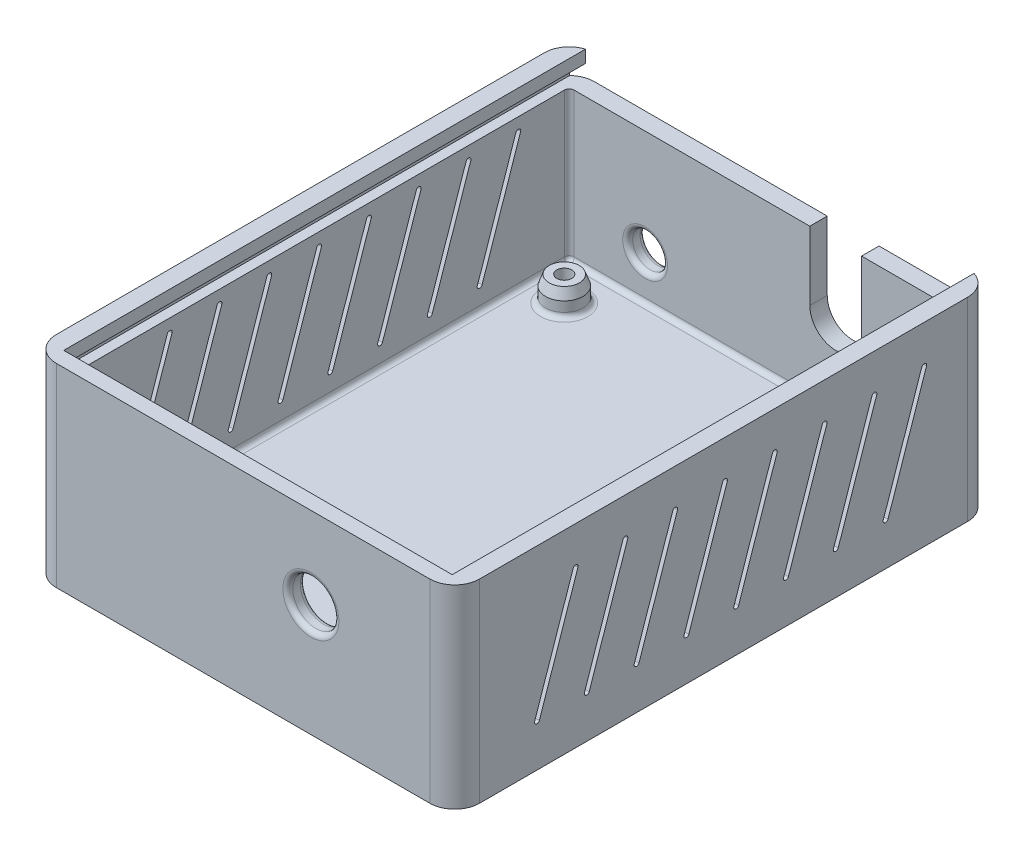
SolidWorks part; units mm, degrees
ref_plane "Front" through (0, 0, 0) normal (0, 0, 1) x (1, 0, 0)
ref_plane "Top" through (0, 0, 0) normal (0, 1, 0) x (1, 0, 0)
ref_plane "Right" through (0, 0, 0) normal (1, 0, 0) x (0, 0, -1)
sketch "Sketch1" plane through (0, 0, 0) normal (0, 1, 0) x (1, 0, 0)
  line L1 (-56.1278, 52.2306) -> (28.8722, 52.2306)
  line L2 (-56.1278, 52.2306) -> (-56.1278, -55.7694)
  line L3 (-56.1278, -55.7694) -> (28.8722, -55.7694)
  line L4 (28.8722, 52.2306) -> (28.8722, -55.7694)
  dimension "D1" = 85
  dimension "D2" = 108
extrude "Boss-Extrude1" add sketch "Sketch1" along normal blind 4
sketch "Sketch2" plane through (0, 4, 0) normal (0, 1, 0) x (1, 0, 0)
  line L0 (-52.6278, 48.7306) -> (-52.6278, -52.2694)
  line L1 (-56.1278, 52.2306) -> (28.8722, 52.2306)
  line L2 (-56.1278, 52.2306) -> (-56.1278, -55.7694)
  line L3 (-56.1278, -55.7694) -> (28.8722, -55.7694)
  line L4 (28.8722, 52.2306) -> (28.8722, -55.7694)
  line L5 (-52.6278, -52.2694) -> (25.3722, -52.2694)
  line L6 (25.3722, 48.7306) -> (25.3722, -52.2694)
  line L7 (-52.6278, 48.7306) -> (25.3722, 48.7306)
  dimension "D1" = 3.5
extrude "Boss-Extrude2" add sketch "Sketch2" along normal blind 35
sketch "Sketch3" plane through (0, 4, 0) normal (0, 1, 0) x (1, 0, 0)
  line L0 (25.3722, 48.7306) -> (-52.6278, 48.7306) construction
  line L1 (-52.6278, 48.7306) -> (-52.6278, -52.2694) construction
  circle A0 centre (-45.6278, 40.7306) radius 3.75
  circle A1 centre (18.3722, 40.7306) radius 3.75
  circle A2 centre (18.3722, -45.2694) radius 3.75
  circle A3 centre (-45.6278, -45.2694) radius 3.75
  point P12 (0, 0)
  point P13 (0, 0)
  point P14 (2.2864, -6.9825)
  dimension "D1" = 2
  dimension "D3" = 8
  dimension "D4" = 7
  dimension "D5" = 86
  dimension "D6" = 64
  dimension "D2" = 2
extrude "Boss-Extrude3" add sketch "Sketch3" along normal blind 5
chamfer "Chamfer1" distance 2 angle 20 4 edges at (18.3722, 9, 49.0194) (-45.6278, 9, 49.0194) (18.3722, 9, -36.9806) (-45.6278, 9, -36.9806)
fillet "Fillet1" radius 5 4 edges at (-56.1278, 19.5, 55.7694) (-56.1278, 19.5, -52.2306) (28.8722, 19.5, -52.2306) (28.8722, 19.5, 55.7694)
sketch "Sketch4" plane through (0, 0, -52.2306) normal (0, 0, -1) x (-1, 0, 0)
  line L0 (-23.8722, 39) -> (51.1278, 39) construction
  line L1 (-27.3722, 36.5) -> (-25.3722, 36.5)
  line L2 (-27.3722, 36.5) -> (-27.3722, 34)
  line L3 (-27.3722, 34) -> (54.6278, 34)
  line L4 (54.6278, 36.5) -> (54.6278, 34)
  line L5 (56.1278, 39) -> (51.1278, 39) construction
  line L7 (-25.3722, 36.5) -> (-25.3722, 39)
  line L8 (-25.3722, 39) -> (52.6278, 39)
  line L9 (52.6278, 36.5) -> (52.6278, 39)
  line L10 (-28.8722, 0) -> (-28.8722, 39) construction
  line L11 (56.1278, 39) -> (56.1278, 0) construction
  line L12 (52.6278, 36.5) -> (54.6278, 36.5)
  dimension "D1" = 2.5
  dimension "D2" = 2.5
  dimension "D3" = 1.5
  dimension "D4" = 1.5
  dimension "D5" = 3.5
  dimension "D6" = 3.5
extrude "Cut-Extrude1" cut sketch "Sketch4" against normal offset from surface (106.5 mm away) 1.5 up to face at (-13.6278, 19.5, 55.7694)
sketch "Sketch5" plane through (0, 0, 54.2694) normal (0, 0, -1) x (-1, 0, 0)
  line L1 (-25.3722, 36.5) -> (52.6278, 36.5)
  line L2 (-25.3722, 36.5) -> (-25.3722, 39)
  line L3 (-25.3722, 39) -> (52.6278, 39)
  line L4 (52.6278, 36.5) -> (52.6278, 39)
extrude "Boss-Extrude4" add sketch "Sketch5" along normal blind 1.5
ref_point "Point1"
ref_point "Point2"
sketch "Sketch6" plane through (0, 0, -52.2306) normal (0, 0, -1) x (-1, 0, 0)
  line L0 (52.6278, 39) -> (-25.3722, 39) construction
  line L5 (-6.0722, 39) -> (4.3278, 39)
  line L6 (-6.0722, 39) -> (-6.0722, 20.2)
  line L8 (4.3278, 39) -> (4.3278, 20.2)
  line L9 (-23.8722, 0) -> (51.1278, 0) construction
  line L10 (-22.3722, 34) -> (-22.3722, 0)
  line L11 (-23.8722, 34) -> (51.1278, 34) construction
  arc A0 (-6.0722, 20.2) -> (4.3278, 20.2) centre (-0.8722, 20.2) ccw
  point P14 (-18.3722, 9)
  dimension "D1" = 5.2
  dimension "D2" = 20.2
  dimension "D3" = 4
  dimension "D4" = 26.7
extrude "Cut-Extrude2" cut sketch "Sketch6" against normal up to next contours L6 A0 L8 L5
sketch "Sketch7" plane through (0, 9, 0) normal (0, 1, 0) x (1, 0, 0)
  circle A0 centre (18.3722, -45.2694) radius 1.5
  circle A1 centre (-45.6278, -45.2694) radius 1.5
  circle A2 centre (18.3722, 40.7306) radius 1.5
  circle A3 centre (-45.6278, 40.7306) radius 1.5
extrude "Cut-Extrude3" cut sketch "Sketch7" against normal blind 4
sketch "Sketch8" plane through (-56.1278, 0, 0) normal (-1, 0, 0) x (0, 0, 1)
  line L0 (-38.025, 31.4771) -> (-30.2771, 8.7047)
  line L2 (-38.9717, 31.155) -> (-31.2238, 8.3826)
  line L3 (-28.025, 31.4771) -> (-20.2771, 8.7047)
  line L4 (-28.9717, 31.155) -> (-21.2238, 8.3826)
  line L5 (-18.025, 31.4771) -> (-10.2771, 8.7047)
  line L6 (-18.9717, 31.155) -> (-11.2238, 8.3826)
  line L7 (-8.025, 31.4771) -> (-0.2771, 8.7047)
  line L8 (-8.9717, 31.155) -> (-1.2238, 8.3826)
  line L9 (1.975, 31.4771) -> (9.7229, 8.7047)
  line L10 (1.0283, 31.155) -> (8.7762, 8.3826)
  line L11 (11.975, 31.4771) -> (19.7229, 8.7047)
  line L12 (11.0283, 31.155) -> (18.7762, 8.3826)
  line L13 (21.975, 31.4771) -> (29.7229, 8.7047)
  line L14 (21.0283, 31.155) -> (28.7762, 8.3826)
  line L15 (31.975, 31.4771) -> (39.7229, 8.7047)
  line L16 (31.0283, 31.155) -> (38.7762, 8.3826)
  arc A4 (-38.025, 31.4771) -> (-38.9717, 31.155) centre (-38.4983, 31.316) ccw
  arc A5 (-30.2771, 8.7047) -> (-31.2238, 8.3826) centre (-30.7504, 8.5437) cw
  arc A6 (-20.2771, 8.7047) -> (-21.2238, 8.3826) centre (-20.7504, 8.5437) cw
  arc A7 (-28.025, 31.4771) -> (-28.9717, 31.155) centre (-28.4983, 31.316) ccw
  arc A8 (-10.2771, 8.7047) -> (-11.2238, 8.3826) centre (-10.7504, 8.5437) cw
  arc A9 (-18.025, 31.4771) -> (-18.9717, 31.155) centre (-18.4983, 31.316) ccw
  arc A10 (-0.2771, 8.7047) -> (-1.2238, 8.3826) centre (-0.7504, 8.5437) cw
  arc A11 (-8.025, 31.4771) -> (-8.9717, 31.155) centre (-8.4983, 31.316) ccw
  arc A12 (9.7229, 8.7047) -> (8.7762, 8.3826) centre (9.2496, 8.5437) cw
  arc A13 (1.975, 31.4771) -> (1.0283, 31.155) centre (1.5017, 31.316) ccw
  arc A14 (19.7229, 8.7047) -> (18.7762, 8.3826) centre (19.2496, 8.5437) cw
  arc A15 (11.975, 31.4771) -> (11.0283, 31.155) centre (11.5017, 31.316) ccw
  arc A16 (29.7229, 8.7047) -> (28.7762, 8.3826) centre (29.2496, 8.5437) cw
  arc A17 (21.975, 31.4771) -> (21.0283, 31.155) centre (21.5017, 31.316) ccw
  arc A18 (39.7229, 8.7047) -> (38.7762, 8.3826) centre (39.2496, 8.5437) cw
  arc A19 (31.975, 31.4771) -> (31.0283, 31.155) centre (31.5017, 31.316) ccw
  point P2 (-30.2771, 8.7047)
  dimension "D1" = 1
  dimension "D2" = 8
extrude "Cut-Extrude4" cut sketch "Sketch8" against normal up to surface (85 mm away) up to face at (28.8722, 19.5, 1.7694)
fillet "Fillet2" radius 1 12 edges at (25.3722, 4, 1.7694) (-13.6278, 4, 52.2694) (-52.6278, 4, 1.7694) (-13.6278, 4, -48.7306) (-45.6278, 4, -36.9806) (18.3722, 4, -36.9806) (18.3722, 4, 49.0194) (-45.6278, 4, 49.0194) (-52.6278, 19, -48.7306) (-52.6278, 19, 52.2694) (25.3722, 19, -48.7306) (25.3722, 19, 52.2694)
sketch "Sketch9" plane through (0, 0, 55.7694) normal (0, 0, 1) x (1, 0, 0)
  circle A0 centre (0, 22.5807) radius 4.625
  point P2 (0, 22.5807)
  dimension "D1" = 9.25
extrude "Cut-Extrude5" cut sketch "Sketch9" against normal up to next
fillet "Fillet3" radius 1 2 edges at (-4.625, 22.5807, 52.2694) (4.625, 22.5807, 55.7694)
sketch "Sketch10" plane through (0, 0, -52.2306) normal (0, 0, -1) x (-1, 0, 0)
  circle A0 centre (37.3967, 12.8776) radius 3.5
  point P2 (37.3967, 12.8776)
  dimension "D1" = 7
extrude "Cut-Extrude6" cut sketch "Sketch10" against normal up to next
fillet "Fillet4" radius 1 2 edges at (-33.8967, 12.8776, -48.7306) (-40.8967, 12.8776, -52.2306)
